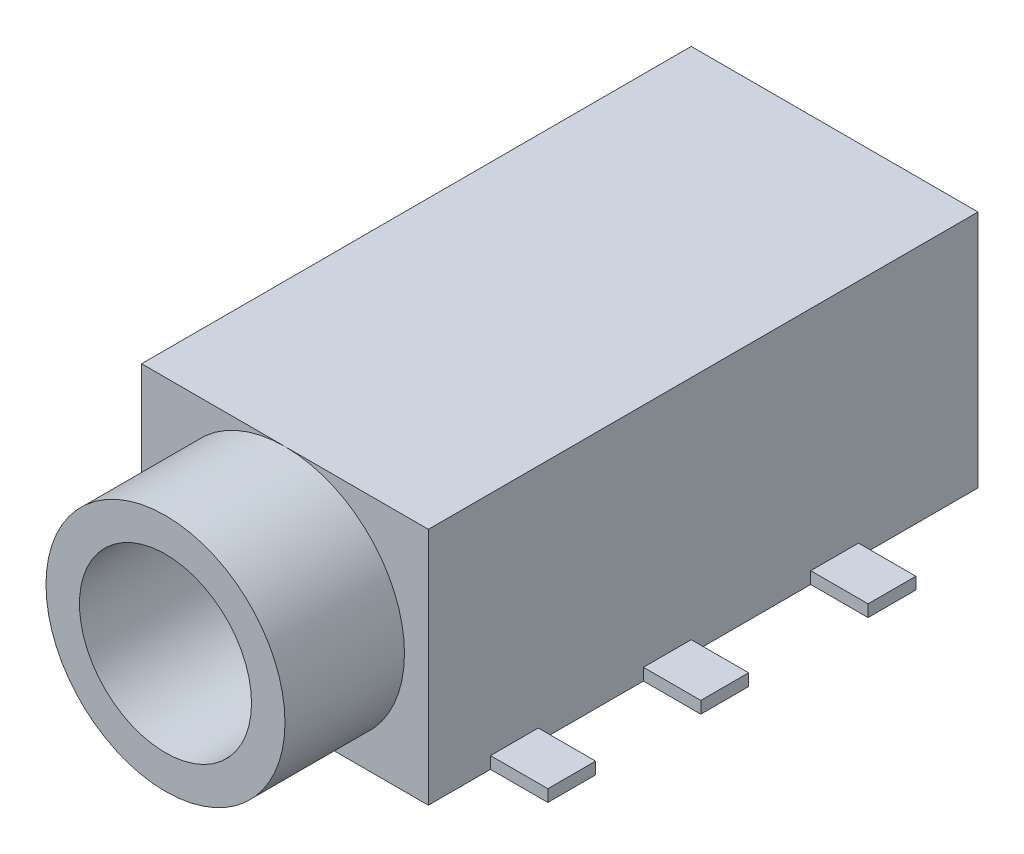
SolidWorks part; units mm, degrees
ref_plane "前视基准面" through (0, 0, 0) normal (0, 0, 1) x (1, 0, 0)
ref_plane "上视基准面" through (0, 0, 0) normal (0, 1, 0) x (1, 0, 0)
ref_plane "右视基准面" through (0, 0, 0) normal (1, 0, 0) x (0, 0, -1)
sketch "草图1" plane through (0, 0, 0) normal (0, 1, 0) x (1, 0, 0)
  line L1 (-3, 0) -> (3, 0)
  line L2 (-3, 0) -> (-3, 11.5)
  line L3 (-3, 11.5) -> (3, 11.5)
  line L4 (3, 0) -> (3, 11.5)
  line L5 (-3, 0) -> (3, 11.5) construction
  line L6 (-3, 11.5) -> (3, 0) construction
  point P0 (0, 5.75)
  point P7 (0, 0)
  dimension "D1" = 6
  dimension "D2" = 11.5
extrude "凸台-拉伸1" add sketch "草图1" along normal blind 5
sketch "草图2" plane through (0, 0, 0) normal (0, 0, 1) x (1, 0, 0)
  line L0 (-3, 5) -> (3, 0) construction
  line L1 (-3, 0) -> (3, 5) construction
  circle A0 centre (0, 2.5) radius 2.5
  point P13 (0, 2.5)
extrude "凸台-拉伸2" add sketch "草图2" along normal blind 2.5
sketch "草图3" plane through (0, 0, 0) normal (0, -1, 0) x (1, 0, 0)
  line L0 (0, 0) -> (0, -2.5) construction
  line L1 (0, -2.5) -> (0, -8.5) construction
  circle A0 centre (0, -2.5) radius 0.75
  circle A1 centre (0, -8.5) radius 0.75
  dimension "D3" = 1.5
  dimension "D1" = 2.5
  dimension "D2" = 6
extrude "凸台-拉伸3" add sketch "草图3" along normal blind 0.5
sketch "草图4" plane through (3, 0, 0) normal (1, 0, 0) x (0, 0, -1)
  line L0 (0, 0) -> (11.5, 0) construction
  line L1 (1.3, 0) -> (2.3, 0)
  line L2 (1.3, 0) -> (1.3, 0.25)
  line L3 (1.3, 0.25) -> (2.3, 0.25)
  line L4 (2.3, 0) -> (2.3, 0.25)
  line L6 (4.5, 0) -> (5.5, 0)
  line L7 (4.5, 0) -> (4.5, 0.25)
  line L8 (4.5, 0.25) -> (5.5, 0.25)
  line L9 (5.5, 0) -> (5.5, 0.25)
  line L10 (8, 0) -> (9, 0)
  line L11 (8, 0) -> (8, 0.25)
  line L12 (8, 0.25) -> (9, 0.25)
  line L13 (9, 0) -> (9, 0.25)
  point P14 (1.8, 0)
  point P16 (5, 0)
  point P17 (8.5, 0)
  dimension "D1" = 1
  dimension "D2" = 1.8
  dimension "D3" = 3.2
  dimension "D4" = 8.5
  dimension "D5" = 0.25
extrude "凸台-拉伸4" add sketch "草图4" along normal blind 1.2
mirror "镜向1" about plane through (0, 0, 0) normal (1, 0, 0) of "凸台-拉伸4"
sketch "草图5" plane through (0, 0, 2.5) normal (0, 0, 1) x (1, 0, 0)
  circle A0 centre (0, 2.5) radius 1.8
  dimension "D1" = 3.6
extrude "切除-拉伸1" cut sketch "草图5" against normal through all
